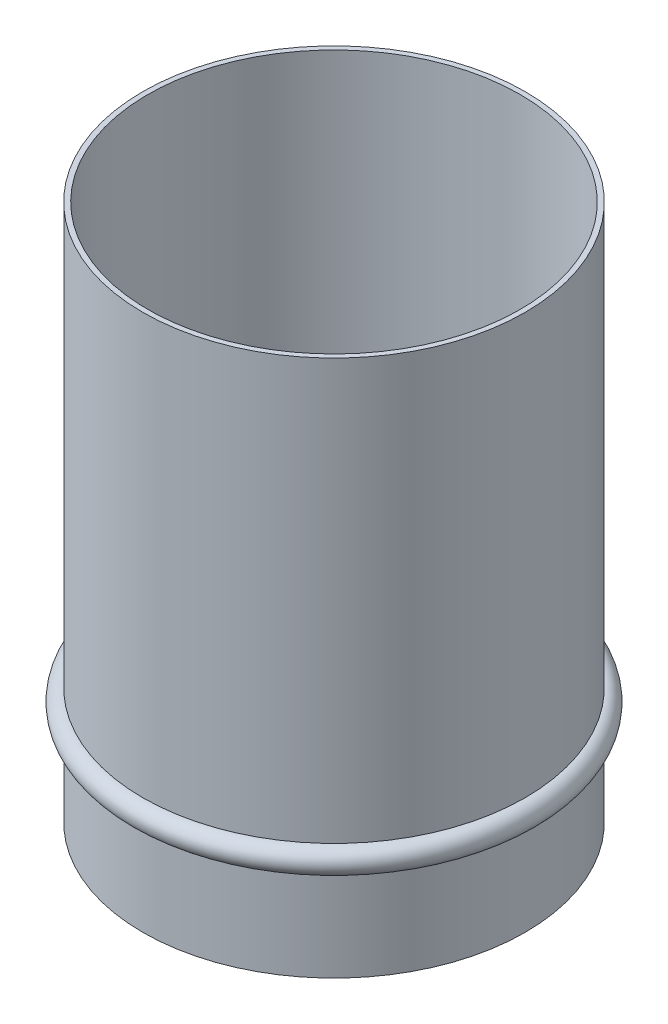
SolidWorks part; units mm, degrees
ref_plane "Front Plane" through (0, 0, 0) normal (0, 0, 1) x (1, 0, 0)
ref_plane "Top Plane" through (0, 0, 0) normal (0, 1, 0) x (1, 0, 0)
ref_plane "Right Plane" through (0, 0, 0) normal (1, 0, 0) x (0, 0, -1)
sketch "Sketch1" plane through (0, 0, 0) normal (0, 0, 1) x (1, 0, 0)
  line L0 (0, -254) -> (0, 254) construction
  line L1 (-177.8, 254) -> (-177.8, -254)
  line L2 (-177.8, -254) -> (0, -254)
  line L3 (-177.8, 254) -> (0, 254) construction
  line L5 (-182.5625, 254) -> (-182.5625, -258.7625)
  line L6 (-182.5625, -258.7625) -> (0, -258.7625)
  line L8 (-177.8, 254) -> (-182.5625, 254)
  line L10 (0, -254) -> (0, -244.1235) construction
  line L11 (-177.8, -254) -> (163.5125, -254) construction
  line L12 (177.8, 203.2) -> (163.5125, -254) construction
  line L13 (182.5602, 203.0512) -> (168.1285, -258.7625) construction
  line L14 (-182.5625, -258.7625) -> (168.1285, -258.7625) construction
  line L15 (0, -254) -> (0, -258.7625)
  circle A0 centre (-182.5625, -159.3215) radius 11.9093
  point P4 (0, 0)
  point P16 (-182.5625, -159.3215)
  dimension "D1" = 177.8
  dimension "D2" = 177.8
  dimension "D3" = 508
  dimension "D4" = 4.7625
revolve "Revolve1" add sketch "Sketch1" angle 360 about L0
